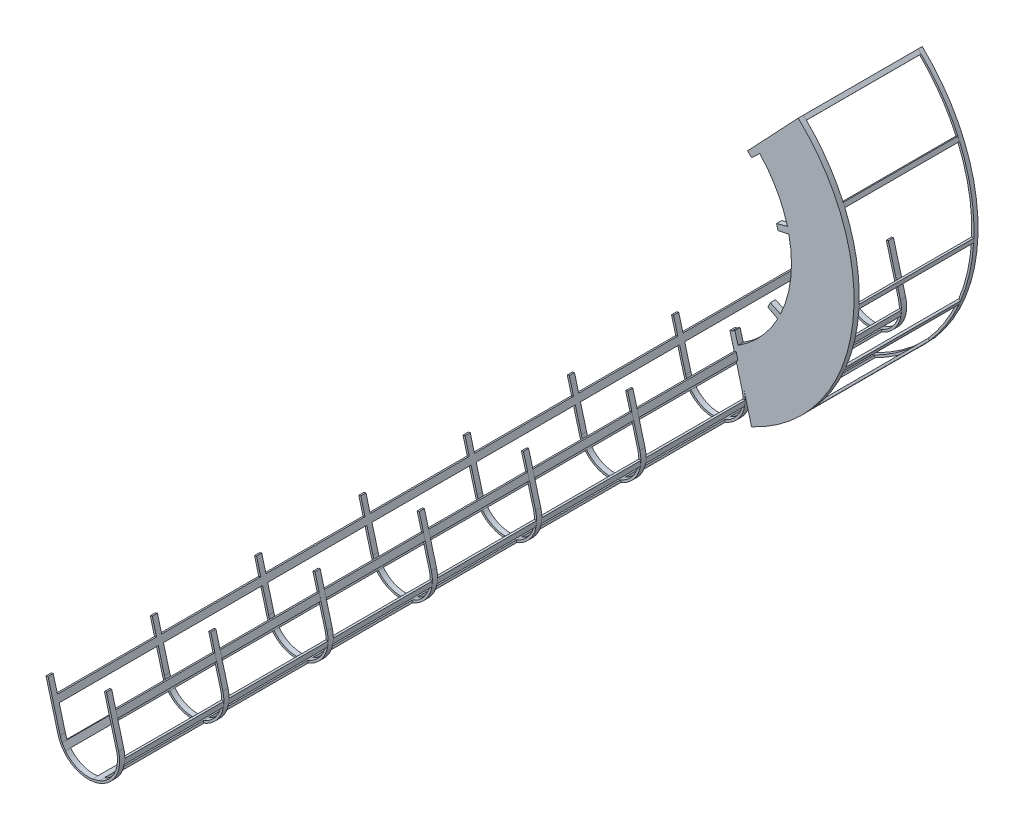
SolidWorks part; units mm, degrees
ref_plane "Front Plane" through (0, 0, 0) normal (0, 0, 1) x (1, 0, 0)
ref_plane "Top Plane" through (0, 0, 0) normal (0, 1, 0) x (1, 0, 0)
ref_plane "Right Plane" through (0, 0, 0) normal (1, 0, 0) x (0, 0, -1)
sketch "Sketch1" plane through (0, 0, 0) normal (0, 0, 1) x (1, 0, 0)
  line L0 (2589.7722, 3641.4613) -> (3126.2405, 1639.3343) construction
  line L1 (2589.7722, 3641.4613) -> (2589.7722, 1790.9207) construction
  line L2 (2589.7722, 3641.4613) -> (4036.1641, 4476.5361) construction
  line L3 (2589.7722, 3641.4613) -> (2589.7722, 4730.9127) construction
  line L4 (3314.7319, 2094.986) -> (3126.4476, 2797.6725)
  line L5 (3276.2421, 4368.6195) -> (3762.2404, 4883.4238)
  line L6 (3155.2199, 2816.6772) -> (3184.6745, 2706.7512)
  line L8 (3314.5991, 4330.3924) -> (3392.8567, 4404.7745)
  line L9 (3554.656, 3904.1383) -> (3658.832, 3932.4989)
  line L10 (4206.4804, 4192.2854) -> (4240.2827, 4080.7423)
  line L11 (3673.0193, 3874.2003) -> (3567.4608, 3851.5207)
  line L12 (3592.7399, 3170.6668) -> (3495.0044, 3216.544)
  line L13 (3470.6748, 3168.1638) -> (3565.7836, 3117.0631)
  arc A0 (908.3583, 3341.4613) -> (915.9883, 3301.4613) centre (2589.7722, 3641.4613) ccw construction
  arc A1 (3314.7319, 2094.986) -> (3762.2404, 4883.4238) centre (2589.7722, 3641.4613) ccw
  arc A2 (3392.8567, 4404.7745) -> (3658.832, 3932.4989) centre (2589.7722, 3641.4613) cw
  circle A3 centre (2589.7722, 3641.4613) radius 1000 construction
  arc A4 (3126.4476, 2797.6725) -> (3155.2199, 2816.6772) centre (2589.7722, 3641.4613) ccw
  arc A5 (3470.6748, 3168.1638) -> (3495.0044, 3216.544) centre (2589.7722, 3641.4613) ccw
  arc A6 (3314.5991, 4330.3924) -> (3276.2421, 4368.6195) centre (2589.7722, 3641.4613) ccw
  arc A7 (3567.4608, 3851.5207) -> (3554.656, 3904.1383) centre (2589.7722, 3641.4613) ccw
  arc A8 (3565.7836, 3117.0631) -> (3184.6745, 2706.7512) centre (2589.7722, 3641.4613) cw
  arc A9 (3673.0193, 3874.2003) -> (3592.7399, 3170.6668) centre (2589.7722, 3641.4613) cw
  dimension "D3" = 600
  dimension "D1" = 300
  dimension "D2" = 195
  dimension "D4" = 300
  dimension "D7" = 60
  dimension "D8" = 560
  dimension "D9" = 60
extrude "Extrude1" add sketch "Sketch1" along normal blind 50 contours A1 L5 A6 L8 A2 L9 A7 L11 A9 L12 A5 L13 A8 L6 A4 L4
sketch "Sketch2" plane through (0, 0, 0) normal (0, 0, -1) x (-1, 0, 0)
  line L0 (-3126.4476, 2797.6725) -> (-3242.649, 2364.0029)
  line L1 (-3314.7319, 2094.986) -> (-3126.4476, 2797.6725) construction
  line L2 (-2546.8921, 2642.3811) -> (-2663.0935, 2208.7114)
  line L3 (-2566.2106, 2647.5575) -> (-2682.4121, 2213.8878)
  line L4 (-3107.1291, 2792.4962) -> (-3223.3305, 2358.8265)
  line L5 (-2566.2106, 2647.5575) -> (-2546.8921, 2642.3811)
  line L6 (-3126.4476, 2797.6725) -> (-3107.1291, 2792.4962)
  arc A0 (-2663.0935, 2208.7114) -> (-3242.649, 2364.0029) centre (-2952.8713, 2286.3571) cw
  arc A1 (-2682.4121, 2213.8878) -> (-3223.3305, 2358.8265) centre (-2952.8713, 2286.3571) cw
  dimension "D1" = 600
  dimension "D2" = 20
extrude "Extrude2" add sketch "Sketch2" against normal blind 50
sketch "Sketch3" plane through (0, 0, 0) normal (0, 0, -1) x (-1, 0, 0)
  line L0 (-2587.6449, 2490.2894) -> (-2604.6311, 2426.8961)
  line L1 (-2587.6449, 2490.2894) -> (-2606.9635, 2495.4658)
  line L2 (-2604.6311, 2426.8961) -> (-2623.9496, 2432.0725)
  line L3 (-2606.9635, 2495.4658) -> (-2623.9496, 2432.0725)
  line L4 (-2663.0935, 2208.7114) -> (-2546.8921, 2642.3811) construction
  line L5 (-2566.2106, 2647.5575) -> (-2682.4121, 2213.8878) construction
  line L6 (-3147.8819, 2640.4045) -> (-3164.8681, 2577.0111)
  line L7 (-3147.8819, 2640.4045) -> (-3167.1348, 2645.5633)
  line L8 (-3164.8681, 2577.0111) -> (-3184.121, 2582.1699)
  line L9 (-3167.1348, 2645.5633) -> (-3184.121, 2582.1699)
  line L10 (-3223.3305, 2358.8265) -> (-3107.1291, 2792.4962) construction
  line L11 (-3062.406, 2007.0685) -> (-2997.6558, 1989.7187)
  line L12 (-3062.406, 2007.0685) -> (-3057.1946, 2026.5175)
  line L13 (-2997.6558, 1989.7187) -> (-2992.4444, 2009.1677)
  line L14 (-3057.1946, 2026.5175) -> (-2992.4444, 2009.1677)
  line L15 (-2733.4037, 2112.4779) -> (-2701.0138, 2164.0142)
  line L16 (-2733.4037, 2112.4779) -> (-2716.3762, 2101.7763)
  line L17 (-2701.0138, 2164.0142) -> (-2683.9863, 2153.3126)
  line L18 (-2716.3762, 2101.7763) -> (-2683.9863, 2153.3126)
  line L19 (-3232.8713, 2286.3571) -> (-3227.8061, 2233.34)
  line L20 (-3232.8713, 2286.3571) -> (-3252.8652, 2284.447)
  line L21 (-3227.8061, 2233.34) -> (-3247.8001, 2231.4298)
  line L22 (-3252.8652, 2284.447) -> (-3247.8001, 2231.4298)
  arc A0 (-3242.649, 2364.0029) -> (-2663.0935, 2208.7114) centre (-2952.8713, 2286.3571) ccw construction
  arc A1 (-3223.3305, 2358.8265) -> (-2682.4121, 2213.8878) centre (-2952.8713, 2286.3571) ccw construction
extrude "Extrude3" add sketch "Sketch3" against normal blind 9000 and the other way blind 1500
pattern_linear "LPattern3" count 10 spacing 1000 along (0, 0, 1) of "Extrude2"
pattern_linear "LPattern4" count 2 spacing 1500 along (0, 0, -1) of "Extrude2"
sketch "Sketch4" plane through (3616.3678, 969.0028, 0) normal (0.9659, 0.2588, 0) x (0, 0, -1)
  line L4 (0, 1670.0735) -> (1450, 1670.0735)
  line L5 (1450, 1670.0735) -> (1450, 1735.7031)
  line L6 (1450, 1735.7031) -> (0, 1735.7031)
  line L7 (0, 1735.7031) -> (0, 1670.0735)
  line L8 (0, 1670.0735) -> (1450, 1670.0735)
  line L9 (1450, 1670.0735) -> (1450, 1735.7031)
  line L10 (1450, 1735.7031) -> (0, 1735.7031)
  line L11 (0, 1735.7031) -> (0, 1670.0735)
  dimension "D1" = 0
extrude "Extrude4" cut sketch "Sketch4" against normal up to next
sketch "Sketch7" plane through (0, 0, 0) normal (0, 0, -1) x (-1, 0, 0)
  line L0 (-3762.2404, 4883.4238) -> (-3791.0032, 4855.6263)
  line L1 (-3762.2404, 4883.4238) -> (-3748.3417, 4869.0424)
  line L2 (-3791.0032, 4855.6263) -> (-3777.1045, 4841.2449)
  line L3 (-3748.3417, 4869.0424) -> (-3777.1045, 4841.2449)
  line L4 (-4143.897, 4349.8742) -> (-4160.0604, 4313.2854)
  line L5 (-4143.897, 4349.8742) -> (-4125.6026, 4341.7925)
  line L6 (-4160.0604, 4313.2854) -> (-4141.766, 4305.2036)
  line L7 (-4125.6026, 4341.7925) -> (-4141.766, 4305.2036)
  line L8 (-4296.5722, 3578.3232) -> (-4294.6227, 3538.3232)
  line L9 (-4296.5722, 3578.3232) -> (-4276.5959, 3579.2968)
  line L10 (-4294.6227, 3538.3232) -> (-4274.6464, 3539.2968)
  line L11 (-4276.5959, 3579.2968) -> (-4274.6464, 3539.2968)
  line L12 (-4170.8044, 2995.3267) -> (-4153.8604, 2955.3267)
  line L13 (-4170.8044, 2995.3267) -> (-4152.3885, 3003.1277)
  line L14 (-4153.8604, 2955.3267) -> (-4135.4445, 2963.1277)
  line L15 (-4152.3885, 3003.1277) -> (-4135.4445, 2963.1277)
  line L16 (-3871.4817, 2512.5799) -> (-3844.694, 2482.8744)
  line L17 (-3871.4817, 2512.5799) -> (-3856.629, 2525.9738)
  line L18 (-3844.694, 2482.8744) -> (-3829.8413, 2496.2682)
  line L19 (-3856.629, 2525.9738) -> (-3829.8413, 2496.2682)
  line L20 (-3314.7319, 2094.986) -> (-3350.7485, 2112.3872)
  line L21 (-3314.7319, 2094.986) -> (-3306.0313, 2112.9943)
  line L22 (-3350.7485, 2112.3872) -> (-3342.0479, 2130.3955)
  line L23 (-3306.0313, 2112.9943) -> (-3342.0479, 2130.3955)
  arc A0 (-3762.2404, 4883.4238) -> (-3314.7319, 2094.986) centre (-2589.7722, 3641.4613) ccw construction
  dimension "D1" = 20
  dimension "D2" = 40
  dimension "D3" = 40
  dimension "D4" = 20
  dimension "D5" = 40
  dimension "D6" = 20
  dimension "D7" = 40
  dimension "D8" = 20
  dimension "D9" = 40
  dimension "D10" = 20
  dimension "D11" = 20
  dimension "D12" = 40
extrude "Extrude6" add sketch "Sketch7" along normal blind 1100
ref_plane "Plane1" through (3748.5101, 4868.8797, 0) normal (0.6865, 0.7272, 0) x (-0.7272, 0.6865, 0)
sketch "Sketch10" plane through (0, 0, -1100) normal (0, 0, -1) x (-1, 0, 0)
  line L0 (-3276.2421, 4368.6195) -> (-3762.2404, 4883.4238) construction
  line L1 (-3276.2421, 4368.6195) -> (-3762.2404, 4883.4238)
  line L2 (-3290.7853, 4354.8901) -> (-3762.9729, 4855.0651)
  line L3 (-3290.7853, 4354.8901) -> (-3276.2421, 4368.6195)
  line L4 (-3306.2427, 2113.0949) -> (-3314.7319, 2094.986)
  arc A0 (-3762.2404, 4883.4238) -> (-3314.7319, 2094.986) centre (-2589.7722, 3641.4613) ccw construction
  arc A1 (-3762.2404, 4883.4238) -> (-3314.7319, 2094.986) centre (-2589.7722, 3641.4613) ccw
  arc A2 (-3762.9729, 4855.0651) -> (-3306.2427, 2113.0949) centre (-2589.7722, 3641.4613) ccw
  dimension "D1" = 20
extrude "Extrude7" add sketch "Sketch10" along normal blind 40
sketch "Sketch11" plane through (0, 0, 9050) normal (0, 0, 1) x (1, 0, 0)
  line L1 (2295.8893, 3000.6449) -> (3347.0071, 3000.6449)
  line L2 (2295.8893, 3000.6449) -> (2295.8893, 1779.6819)
  line L3 (2295.8893, 1779.6819) -> (3347.0071, 1779.6819)
  line L4 (3347.0071, 3000.6449) -> (3347.0071, 1779.6819)
extrude "Extrude8" cut sketch "Sketch11" against normal up to surface (3000 mm away) up to face at (2659.4214, 2266.3225, 6050)
